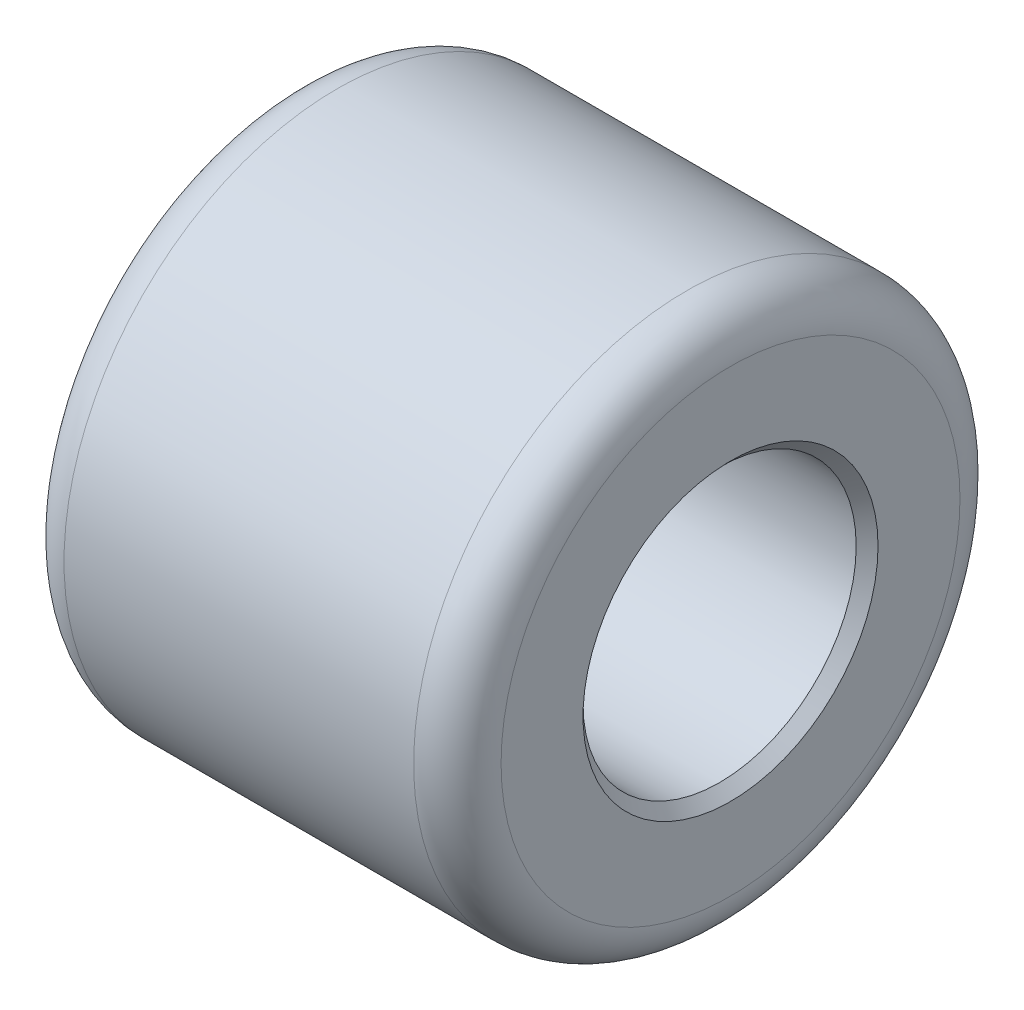
SolidWorks part; units mm, degrees
material "Balsa"
ref_plane "Front Plane" through (0, 0, 0) normal (0, 0, 1) x (1, 0, 0)
ref_plane "Top Plane" through (0, 0, 0) normal (0, 1, 0) x (1, 0, 0)
ref_plane "Right Plane" through (0, 0, 0) normal (1, 0, 0) x (0, 0, -1)
sketch "Sketch1" plane through (0, 0, 0) normal (1, 0, 0) x (0, 0, -1)
  circle A0 centre (0, 0) radius 312.5
  circle A1 centre (0, 0) radius 156.25
  dimension "D1" = 625
  dimension "D2" = 312.5
extrude "Boss-Extrude1" add sketch "Sketch1" along normal blind 500
chamfer "Chamfer1" distance 12.5 angle 45 2 edges at (0, 0, -156.25) (500, 0, -156.25)
fillet "Fillet1" radius 50 2 edges at (0, 0, -312.5) (500, 0, -312.5)
